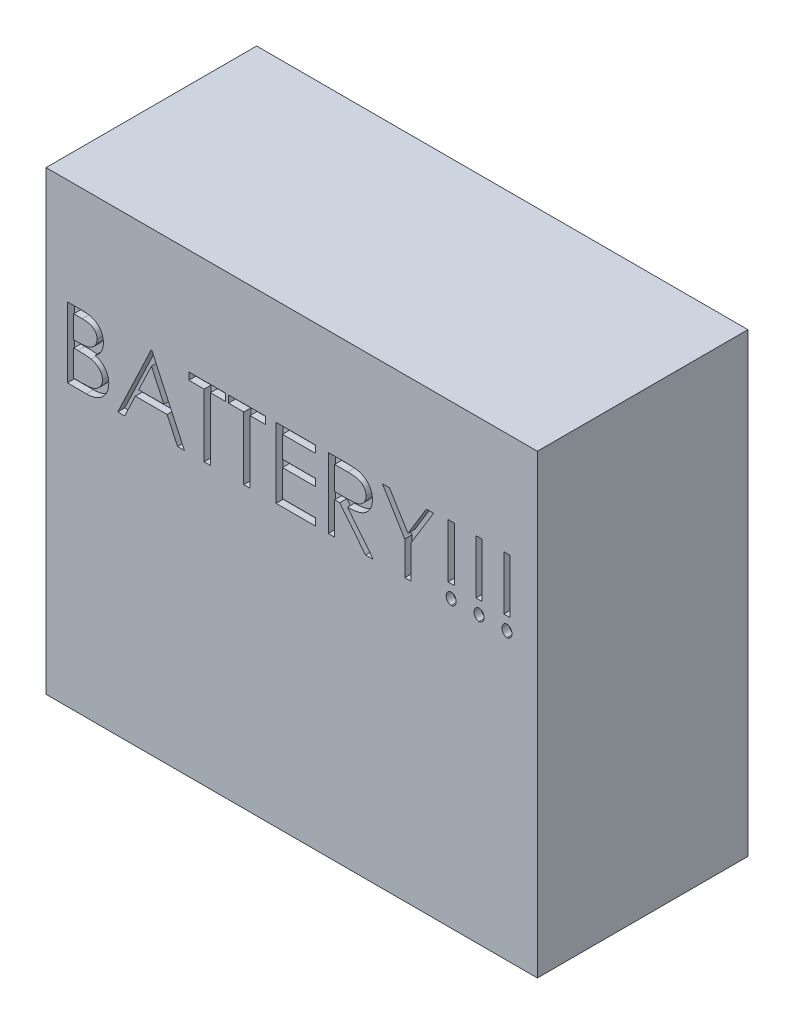
SolidWorks part; units mm, degrees
ref_plane "Front Plane" through (0, 0, 0) normal (0, 0, 1) x (1, 0, 0)
ref_plane "Top Plane" through (0, 0, 0) normal (0, 1, 0) x (1, 0, 0)
ref_plane "Right Plane" through (0, 0, 0) normal (1, 0, 0) x (0, 0, -1)
sketch "Sketch1" plane through (0, 0, 0) normal (0, 1, 0) x (1, 0, 0)
  line L0 (-88.9, 38.1) -> (88.9, -38.1) construction
  line L1 (-88.9, 38.1) -> (88.9, 38.1)
  line L2 (-88.9, 38.1) -> (-88.9, -38.1)
  line L3 (-88.9, -38.1) -> (88.9, -38.1)
  line L4 (88.9, 38.1) -> (88.9, -38.1)
  dimension "D1" = 177.8
  dimension "D2" = 76.2
extrude "Boss-Extrude1" add sketch "Sketch1" along normal mid plane 165.1
sketch "Sketch2" plane through (0, 0, 38.1) normal (0, 0, 1) x (1, 0, 0)
  text T0 "BATTERY!!!" font "Century Gothic" height 25.4
extrude "Cut-Extrude1" cut sketch "Sketch2" against normal blind 2.54
